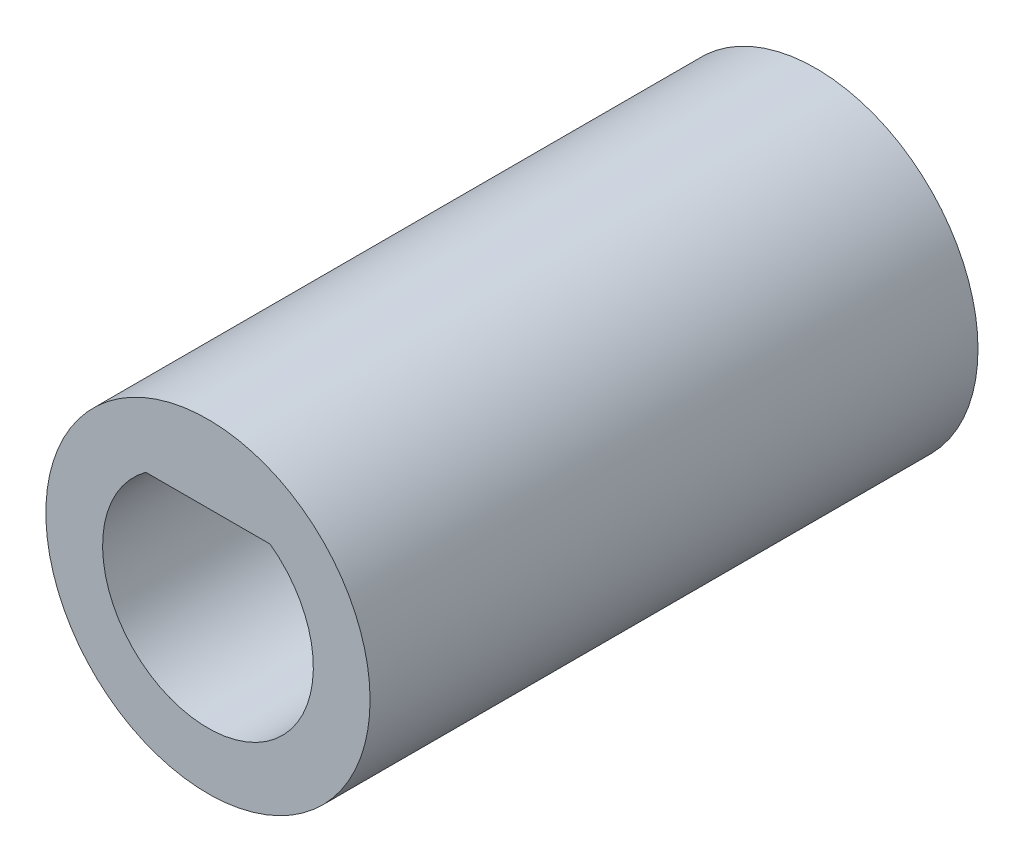
SolidWorks part; units mm, degrees
material "ABS"
ref_plane "Alzado" through (0, 0, 0) normal (0, 0, 1) x (1, 0, 0)
ref_plane "Planta" through (0, 0, 0) normal (0, 1, 0) x (1, 0, 0)
ref_plane "Vista lateral" through (0, 0, 0) normal (1, 0, 0) x (0, 0, -1)
sketch "Croquis1" plane through (0, 0, 0) normal (0, 0, 1) x (1, 0, 0)
  circle A0 centre (0, 0) radius 4
  dimension "D1" = 8
extrude "Saliente-Extruir1" add sketch "Croquis1" along normal mid plane 15
sketch "Croquis2" plane through (0, 0, 7.5) normal (0, 0, 1) x (1, 0, 0)
  line L1 (1.5, 2) -> (-1.5, 2) construction
  line L2 (-1.533, 2.1) -> (1.533, 2.1)
  arc A0 (-1.5, 2) -> (1.5, 2) centre (0, 0) ccw construction
  arc A1 (-1.533, 2.1) -> (1.533, 2.1) centre (0, 0) ccw
  dimension "D1" = 5
  dimension "D3" = 0.1
  dimension "D2" = 3
  dimension "D4" = 0.1
extrude "Cortar-Extruir1" cut sketch "Croquis2" against normal blind 7.5
sketch "Croquis3" plane through (0, 0, -7.5) normal (0, 0, -1) x (-1, 0, 0)
  line L0 (-2.9287, 0.65) -> (2.9287, 0.65)
  line L1 (-2.9287, -0.65) -> (2.9287, -0.65)
  line L2 (0, -0.65) -> (0, 0.65) construction
  arc A0 (-2.9287, -0.65) -> (2.9287, -0.65) centre (0, 0) ccw
  arc A1 (2.9287, 0.65) -> (-2.9287, 0.65) centre (0, 0) ccw
  dimension "D1" = 6
  dimension "D2" = 1.3
extrude "Cortar-Extruir2" cut sketch "Croquis3" against normal blind 7.5
